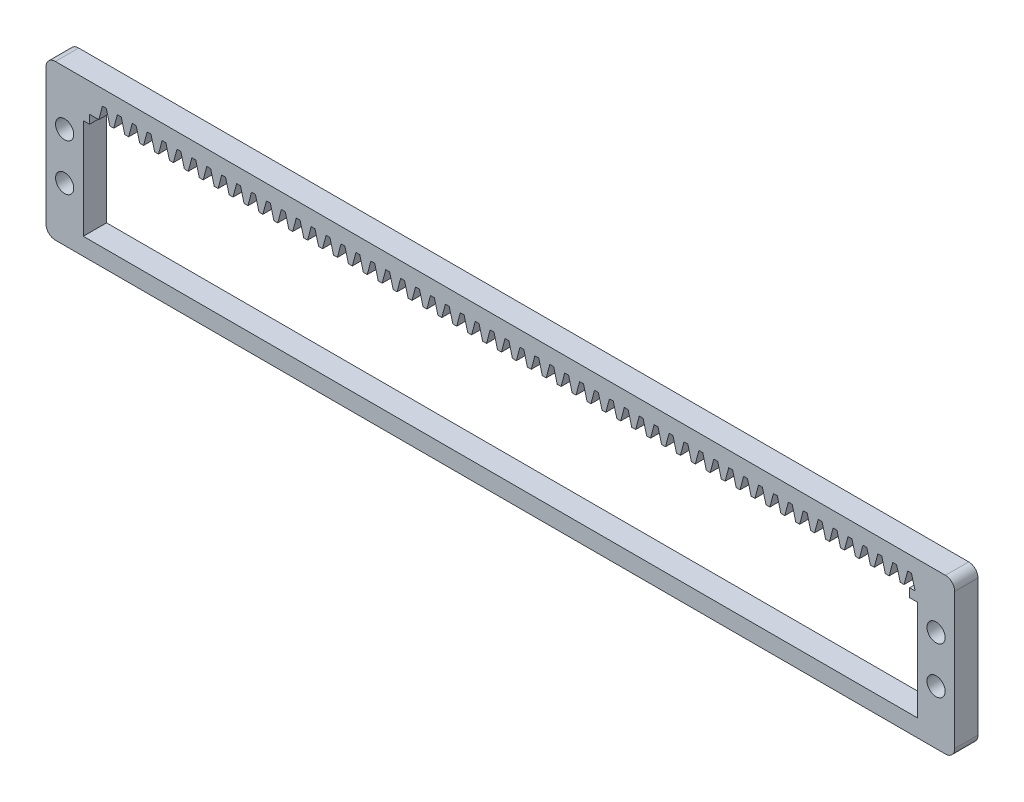
SolidWorks part; units mm, degrees
other "Markup1"
sketch "Sketch6" plane through (0, -30, 3.6) normal (0, 0, 1) x (1, 0, 0)
other "Markup2"
sketch "Sketch7" plane through (0, -30, 3.6) normal (0, 0, 1) x (1, 0, 0)
ref_plane "Front Plane" through (0, 0, 0) normal (0, 0, 1) x (1, 0, 0)
ref_plane "Top Plane" through (0, 0, 0) normal (0, 1, 0) x (1, 0, 0)
ref_plane "Right Plane" through (0, 0, 0) normal (1, 0, 0) x (0, 0, -1)
sketch "Sketch1" plane through (0, 0, 0) normal (0, 0, 1) x (1, 0, 0)
  line L1 (2, 0) -> (193, 0)
  line L2 (0, -2) -> (0, -31.22)
  line L3 (2, -33.22) -> (193, -33.22)
  line L4 (195, -2) -> (195, -31.22)
  arc A0 (193, -33.22) -> (195, -31.22) centre (193, -31.22) ccw
  arc A1 (0, -31.22) -> (2, -33.22) centre (2, -31.22) ccw
  arc A2 (2, 0) -> (0, -2) centre (2, -2) ccw
  arc A3 (193, 0) -> (195, -2) centre (193, -2) cw
  point P7 (195, -33.22)
  point P12 (0, 0)
  point P15 (195, 0)
  dimension "D3" = 2
  dimension "D1" = 33.22
  dimension "D2" = 195
extrude "Boss-Extrude1" add sketch "Sketch1" along normal blind 5
sketch "Sketch2" plane through (0, 0, 5) normal (0, 0, 1) x (1, 0, 0)
  line L0 (2, -33.22) -> (193, -33.22) construction
  line L1 (8, -8) -> (187, -8)
  line L2 (8, -8) -> (8, -29.5)
  line L3 (8, -29.5) -> (187, -29.5)
  line L4 (187, -8) -> (187, -29.5)
  line L5 (0, -2) -> (0, -31.22) construction
  line L7 (195, -31.22) -> (195, -2) construction
  line L8 (8, -18.75) -> (187, -18.75) construction
  line L12 (8, -29.5) -> (187, -29.5) construction
  line L13 (187, -4.3144) -> (187, -29.5) construction
  dimension "D1" = 21.5
  dimension "D2" = 8
  dimension "D3" = 8
  dimension "D4" = 3.72
extrude "Cut-Extrude1" cut sketch "Sketch2" against normal through all
sketch "Sketch3" plane through (0, 0, 5) normal (0, 0, 1) x (1, 0, 0)
  line L0 (187, -8) -> (8, -8) construction
  line L1 (9.35, -8) -> (185.32, -8)
  line L2 (9.35, -8) -> (9.35, -6.15)
  line L3 (9.35, -6.15) -> (185.32, -6.15)
  line L4 (185.32, -8) -> (185.32, -6.15)
  line L5 (187, -29.5) -> (187, -8) construction
  line L6 (8, -8) -> (8, -29.5) construction
  dimension "D1" = 1.85
  dimension "D2" = 1.68
  dimension "D3" = 1.35
extrude "Cut-Extrude2" cut sketch "Sketch3" against normal through all
sketch "Sketch4" plane through (0, 0, 5) normal (0, 0, 1) x (1, 0, 0)
  line L0 (187.7, -6.15) -> (186.5, -6.15) construction
  line L1 (185.32, -6.15) -> (9.35, -6.15) construction
  line L2 (187.7, -6.15) -> (188.465, -3.2492) construction
  line L3 (188.465, -3.2492) -> (185.735, -3.2492) construction
  line L4 (185.735, -3.2492) -> (186.5, -6.15)
  line L5 (185.735, -3.2492) -> (184.905, -3.2492)
  line L6 (184.905, -3.2492) -> (184.14, -6.15)
  line L7 (184.14, -6.15) -> (186.5, -6.15)
  line L10 (186.5, -6.15) -> (187.7, -6.15) construction
  dimension "D1" = 1.2
  dimension "D3" = 3
  dimension "D4" = 0.83
  dimension "D5" = 2.73
extrude "Cut-Extrude4" cut sketch "Sketch4" against normal through all
pattern_linear "LPattern1" count 55 spacing 3.2 along (-1, 0, 0) of "Cut-Extrude4"
sketch "Sketch5" plane through (0, 0, 5) normal (0, 0, 1) x (1, 0, 0)
  line L0 (187, -16.61) -> (195, -16.61) construction
  line L1 (193, 0) -> (2, 0) construction
  line L2 (8, -8) -> (8, -29.5) construction
  line L3 (0, -2) -> (0, -31.22) construction
  line L4 (2, -33.22) -> (193, -33.22) construction
  line L5 (0, -16.61) -> (8, -16.61) construction
  line L7 (191, -11.61) -> (191, -21.61) construction
  line L8 (4, -11.61) -> (4, -21.61) construction
  line L9 (187, -29.5) -> (187, -8) construction
  line L10 (195, -31.22) -> (195, -2) construction
  circle A4 centre (4, -11.61) radius 1.95
  circle A5 centre (4, -21.61) radius 1.95
  circle A6 centre (191, -11.61) radius 1.95
  circle A7 centre (191, -21.61) radius 1.95
  point P8 (191, -16.61)
  point P31 (191, -16.61)
  dimension "D1" = 3.9
  dimension "D2" = 4
  dimension "D3" = 3.9
  dimension "D4" = 3.9
  dimension "D6" = 3.9
  dimension "D5" = 10
  dimension "D7" = 10
extrude "Cut-Extrude5" cut sketch "Sketch5" against normal blind 10
